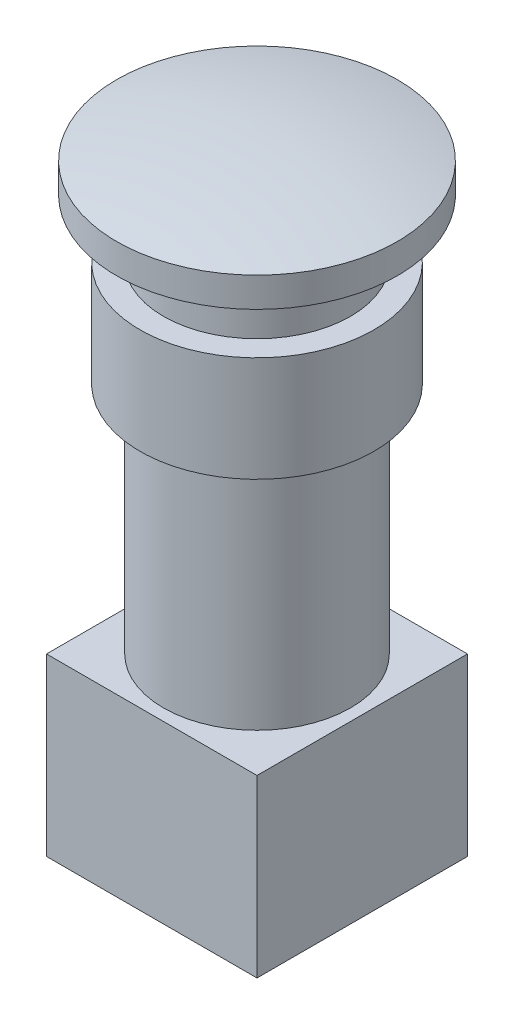
SolidWorks part; units mm, degrees
material "ABS"
ref_plane "Plan de face" through (0, 0, 0) normal (0, 0, 1) x (1, 0, 0)
ref_plane "Plan de dessus" through (0, 0, 0) normal (0, 1, 0) x (1, 0, 0)
ref_plane "Plan de droite" through (0, 0, 0) normal (1, 0, 0) x (0, 0, -1)
sketch "Esquisse1" plane through (0, 0, 0) normal (0, 0, 1) x (1, 0, 0)
  line L0 (0, 0) -> (0, 40.7903) construction
  line L1 (-12, 36.5386) -> (-12, 34)
  line L2 (-12, 34) -> (-8, 34)
  line L3 (-8, 34) -> (-8, 29)
  line L4 (-8, 0) -> (0, 0)
  line L5 (0, 0) -> (0, 38)
  line L6 (-8, 29) -> (-10, 29)
  line L7 (-10, 29) -> (-10, 20)
  line L8 (-10, 20) -> (-8, 20)
  line L9 (-8, 20) -> (-8, 0)
  arc A0 (-12, 36.5386) -> (0, 38) centre (0, -12) cw
  dimension "D3" = 50
  dimension "D1" = 38
  dimension "D2" = 12
  dimension "D4" = 8
  dimension "D5" = 4
  dimension "D6" = 18
  dimension "D7" = 10
  dimension "D8" = 9
revolve "Révolution1" add sketch "Esquisse1" angle 360 about L0
sketch "Esquisse2" plane through (0, 0, 0) normal (0, -1, 0) x (1, 0, 0)
  line L0 (-9, 9) -> (9, -9) construction
  line L1 (-9, 9) -> (9, 9)
  line L2 (-9, 9) -> (-9, -9)
  line L3 (-9, -9) -> (9, -9)
  line L4 (9, 9) -> (9, -9)
  dimension "D1" = 18
extrude "Extrusion1" add sketch "Esquisse2" along normal blind 15
